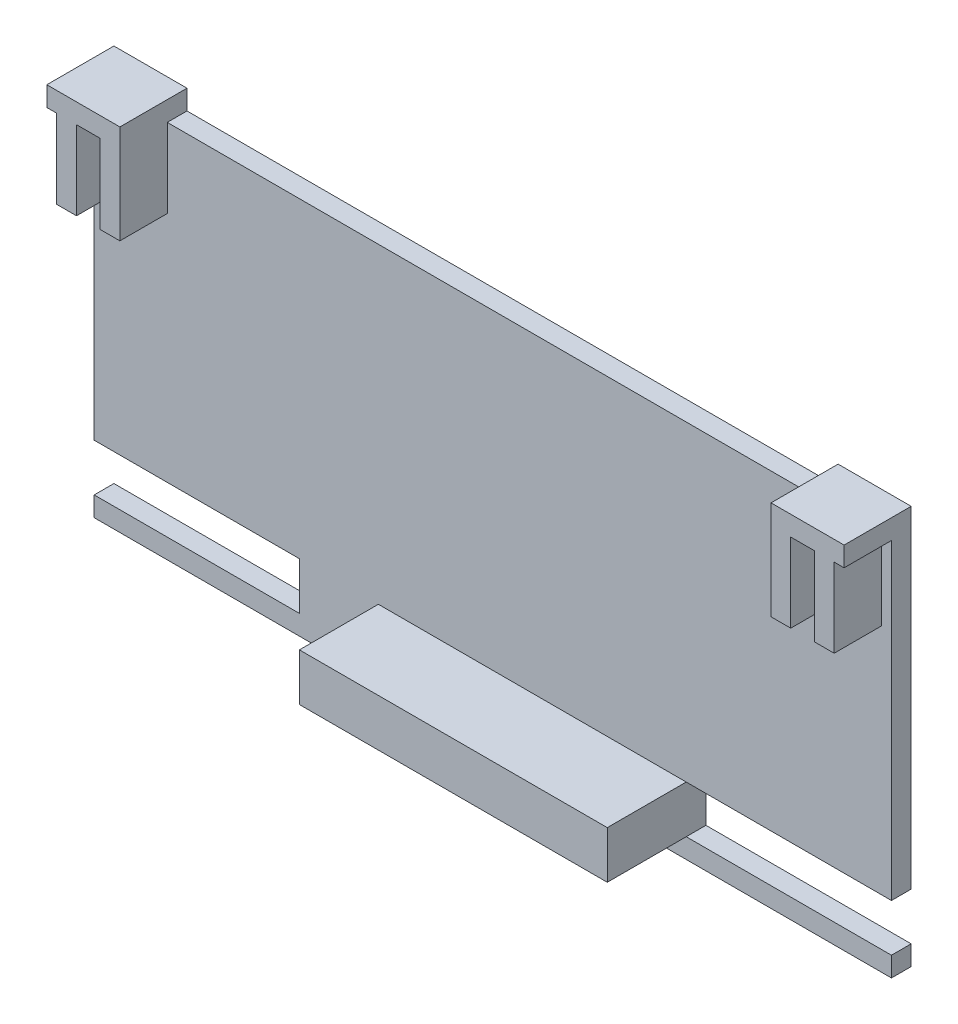
SolidWorks part; units mm, degrees
ref_plane "Front" through (0, 0, 0) normal (0, 0, 1) x (1, 0, 0)
ref_plane "Top" through (0, 0, 0) normal (0, 1, 0) x (1, 0, 0)
ref_plane "Right" through (0, 0, 0) normal (1, 0, 0) x (0, 0, -1)
sketch "Sketch1" plane through (0, 0, 0) normal (0, 0, 1) x (1, 0, 0)
  line L0 (-1.25, 0) -> (-1.25, 24)
  line L1 (-1.25, 0) -> (49.25, 0)
  line L2 (0, 0) -> (0, 22.75) construction
  line L3 (-1.25, 22.75) -> (49.25, 22.75) construction
  line L4 (48, 0) -> (48, 22.75) construction
  line L5 (-1.25, 24) -> (49.25, 24)
  line L6 (49.25, 0) -> (49.25, 24)
  line L7 (-1.25, 0) -> (-1.25, 22.75) construction
  line L8 (49.25, 0) -> (49.25, 22.75) construction
  dimension "D1" = 22.75
  dimension "D2" = 48
  dimension "D3" = 1.25
  dimension "D4" = 1.25
  dimension "D5" = 1.25
extrude "Boss-Extrude1" add sketch "Sketch1" along normal blind 1.25
sketch "Sketch2" plane through (0, 24, 0) normal (0, 1, 0) x (1, 0, 0)
  line L0 (49.25, -1.25) -> (-1.25, -1.25) construction
  line L1 (47.3715, -1.25) -> (48.6215, -1.25)
  line L2 (47.3715, -1.25) -> (47.3715, -4.25)
  line L3 (47.3715, -4.25) -> (48.6215, -4.25)
  line L4 (48.6215, -1.25) -> (48.6215, -4.25)
  line L6 (45.8715, -1.25) -> (44.6215, -1.25)
  line L7 (45.8715, -1.25) -> (45.8715, -4.25)
  line L8 (45.8715, -4.25) -> (44.6215, -4.25)
  line L9 (44.6215, -1.25) -> (44.6215, -4.25)
  line L10 (24, 0) -> (24, 4.2372) construction
  line L11 (49.25, 0) -> (-1.25, 0) construction
  line L12 (3.3785, -1.25) -> (3.3785, -4.25)
  line L13 (2.1285, -4.25) -> (3.3785, -4.25)
  line L14 (2.1285, -1.25) -> (2.1285, -4.25)
  line L15 (2.1285, -1.25) -> (3.3785, -1.25)
  line L16 (-0.6215, -1.25) -> (-0.6215, -4.25)
  line L17 (0.6285, -4.25) -> (-0.6215, -4.25)
  line L18 (0.6285, -1.25) -> (0.6285, -4.25)
  line L19 (0.6285, -1.25) -> (-0.6215, -1.25)
  dimension "D1" = 1.5
  dimension "D2" = 3
  dimension "D3" = 1.25
extrude "Boss-Extrude2" add sketch "Sketch2" against normal blind 5
sketch "Sketch3" plane through (0, 0, 0) normal (0, 0, -1) x (-1, 0, 0)
  line L0 (-49.25, 0) -> (-49.25, 24) construction
  line L1 (-49.25, 1.25) -> (-36.25, 1.25)
  line L2 (-49.25, 1.25) -> (-49.25, 4.25)
  line L3 (-49.25, 4.25) -> (-36.25, 4.25)
  line L4 (-36.25, 1.25) -> (-36.25, 4.25)
  line L5 (1.25, 0) -> (-49.25, 0) construction
  line L6 (-24, 0) -> (-24, 7.297) construction
  line L7 (-11.75, 1.25) -> (-11.75, 4.25)
  line L8 (1.25, 1.25) -> (-11.75, 1.25)
  line L9 (1.25, 4.25) -> (-11.75, 4.25)
  line L10 (1.25, 1.25) -> (1.25, 4.25)
  dimension "D1" = 3
  dimension "D2" = 1.25
  dimension "D3" = 13
extrude "Cut-Extrude1" cut sketch "Sketch3" against normal up to surface (1.25 mm away) up to face at (25.1375, 19.35, 1.25)
sketch "Sketch5" plane through (0, 24, 0) normal (0, 1, 0) x (1, 0, 0)
  line L1 (3.3785, 0) -> (-1.25, 0)
  line L2 (44.6215, -4.25) -> (49.25, -4.25)
  line L3 (44.6215, -4.25) -> (44.6215, 0)
  line L4 (44.6215, 0) -> (49.25, 0)
  line L5 (24, -1.25) -> (24, 0) construction
  line L6 (44.6215, -1.25) -> (3.3785, -1.25) construction
  line L7 (49.25, 0) -> (-1.25, 0) construction
  line L8 (49.25, -4.25) -> (49.25, 0)
  line L9 (3.3785, -4.25) -> (3.3785, 0)
  line L10 (3.3785, -4.25) -> (-1.25, -4.25)
  line L11 (-1.25, -4.25) -> (-1.25, 0)
extrude "Boss-Extrude3" add sketch "Sketch5" along normal blind 1.25
sketch "Sketch9" plane through (0, 0, 1.25) normal (0, 0, 1) x (1, 0, 0)
  line L0 (16.75, 1.25) -> (36.25, 1.25)
  line L1 (16.75, 1.25) -> (16.75, 4.25)
  line L2 (36.25, 1.25) -> (36.25, 4.25)
  line L3 (16.75, 4.25) -> (36.25, 4.25)
  line L4 (49.25, 1.25) -> (36.25, 1.25) construction
  dimension "D1" = 19.5
extrude "Boss-Extrude5" add sketch "Sketch9" along normal blind 5
